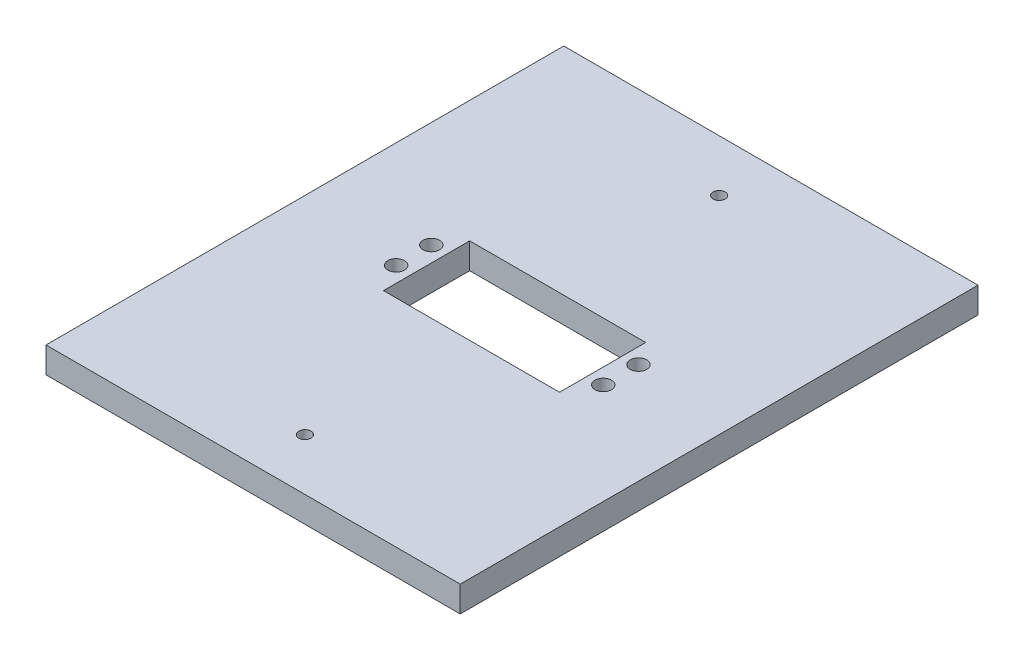
SolidWorks part; units mm, degrees
ref_plane "Front Plane" through (0, 0, 0) normal (0, 0, 1) x (1, 0, 0)
ref_plane "Top Plane" through (0, 0, 0) normal (0, 1, 0) x (1, 0, 0)
ref_plane "Right Plane" through (0, 0, 0) normal (1, 0, 0) x (0, 0, -1)
sketch "Sketch1" plane through (0, 0, 0) normal (0, 1, 0) x (1, 0, 0)
  line L0 (101.6, 120.65) -> (0, 120.65) construction
  line L1 (0, 0) -> (185.42, 0) construction
  line L2 (0, 0) -> (0, 241.3) construction
  line L3 (0, 241.3) -> (185.42, 241.3) construction
  line L4 (185.42, 0) -> (185.42, 241.3) construction
  line L5 (134.62, 57.15) -> (134.62, 0) construction
  line L6 (185.42, 184.15) -> (83.82, 184.15)
  line L7 (185.42, 184.15) -> (185.42, 57.15)
  line L8 (185.42, 57.15) -> (83.82, 57.15)
  line L9 (83.82, 184.15) -> (83.82, 57.15)
  line L10 (134.62, 184.15) -> (134.62, 241.3) construction
  circle A0 centre (145.415, 120.65) radius 43.815 construction
  dimension "D3" = 87.63
  dimension "D1" = 185.42
  dimension "D2" = 241.3
  dimension "D4" = 101.6
  dimension "D5" = 127
  dimension "D6" = 101.6
extrude "Boss-Extrude1" add sketch "Sketch1" along normal blind 6.35
sketch "Sketch2" plane through (0, 6.35, 0) normal (0, 1, 0) x (1, 0, 0)
  line L9 (113.665, 131.2227) -> (156.845, 131.2227)
  line L10 (114.935, 129.9527) -> (155.575, 129.9527) construction
  line L11 (114.935, 129.9527) -> (114.935, 111.3473) construction
  line L12 (114.935, 111.3473) -> (155.575, 111.3473) construction
  line L14 (155.575, 129.9527) -> (155.575, 111.3473) construction
  line L15 (156.845, 131.2227) -> (156.845, 110.0773)
  line L16 (113.665, 110.0773) -> (156.845, 110.0773)
  line L17 (113.665, 131.2227) -> (113.665, 110.0773)
  line B0 (155.575, 121.3168) -> (155.575, 112.6808) construction
  line B1 (135.255, 129.9527) -> (155.575, 129.9528) construction
  line B2 (135.255, 111.3472) -> (155.575, 129.9528) construction
  line B3 (135.255, 129.9527) -> (155.575, 111.3473) construction
  line B4 (114.935, 112.6807) -> (114.935, 129.9527) construction
  circle B5 centre (109.855, 116.9987) radius 2.032
  circle B6 centre (109.855, 125.6347) radius 2.032
  circle B7 centre (160.655, 125.6348) radius 2.032
  circle B8 centre (160.655, 116.9988) radius 2.032
  circle B9 centre (145.415, 120.65) radius 3.81 construction
  line B10 (109.855, 127.6667) -> (109.855, 129.9527) construction
  line B11 (109.855, 114.9667) -> (109.855, 112.6807) construction
  dimension "D2" = 1.27
sketch_block_instance "Block-motorBasic-1"
sketch_block "Block-motorBasic" parameters "D2"=4.064, "D3"=7.62, "D5"=4.064, "D1"=6.35, "D4"=1.27
extrude "Cut-Extrude1" cut sketch "Sketch2" against normal through all
sketch "Sketch7" plane through (0, 6.35, 0) normal (0, 1, 0) x (1, 0, 0)
  line L0 (134.62, 184.15) -> (134.62, 57.15) construction
  line L1 (185.42, 184.15) -> (83.82, 184.15) construction
  line L2 (83.82, 57.15) -> (185.42, 57.15) construction
  line L3 (134.62, 120.65) -> (185.42, 120.65) construction
  line L4 (185.42, 57.15) -> (185.42, 184.15) construction
  line L6 (185.42, 184.15) -> (83.82, 184.15) construction
  circle A0 centre (134.62, 171.45) radius 1.5
  circle A1 centre (134.62, 69.85) radius 1.5
  dimension "D1" = 3
  dimension "D2" = 12.7
extrude "Cut-Extrude2" cut sketch "Sketch7" against normal through all
equation "\"flipWidth\"= 6.5"
equation "\"flipHeight\"= 4"
equation "\"spindleLength\"= 7.75"
equation "\"bearingID\"= 0.1559"
equation "\"motorWidth\"= 0.79"
equation "\"motorHeight\"= 1.0"
equation "\"motorLength\"= 1.58"
equation "\"depth\"= 7.3"
equation "\"height\"= 9.5"
equation "\"width\"= 8.60"
equation "\"bearingOD\"= 0.3539\t"
equation "\"spindleMaxDiam\"= 2.75"
equation "\"totalLength\"= 15"
equation "\"stopperWidth\"= 0.13"
equation "\"stopperHeight\"= 0.31"
equation "\"stopperLength\"= 8.73"
equation "\"D2@Sketch1\"=\"height\""
equation "\"D1@Sketch1\"=\"depth\""
equation "\"D3@Sketch1\"=\"spindleMaxDiam\"+0.7"
